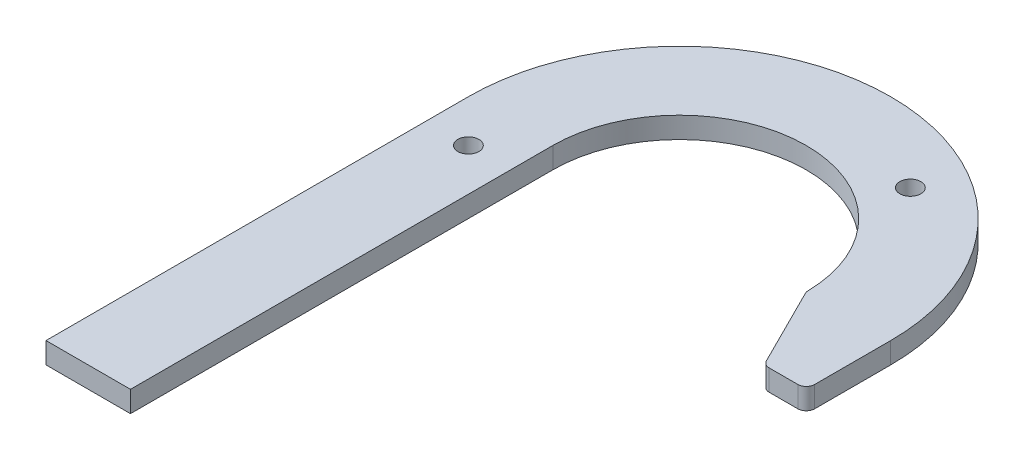
SolidWorks part; units mm, degrees
ref_plane "Front Plane" through (0, 0, 0) normal (0, 0, 1) x (1, 0, 0)
ref_plane "Top Plane" through (0, 0, 0) normal (0, 1, 0) x (1, 0, 0)
ref_plane "Right Plane" through (0, 0, 0) normal (1, 0, 0) x (0, 0, -1)
ref_plane "Plane1" through (0, 6.35, 0) normal (0, 1, 0) x (1, 0, 0)
sketch "Sketch1" plane through (0, 6.35, 0) normal (0, 1, 0) x (1, 0, 0)
  line L0 (90.4698, 44.1178) -> (99.06, 44.1178)
  line L1 (101.6, 46.6578) -> (101.6, 69.5178)
  line L2 (-25.4, 69.5178) -> (-25.4, -57.4822)
  line L3 (-25.4, -57.4822) -> (0, -57.4822)
  line L4 (0, -57.4822) -> (0, 69.5178)
  line L5 (76.4636, 68.9906) -> (88.198, 45.5218)
  circle A0 centre (64.7438, 112.2707) radius 3.175
  arc A1 (99.06, 44.1178) -> (101.6, 46.6578) centre (99.06, 46.6578) ccw
  arc A2 (101.6, 69.5178) -> (-25.4, 69.5178) centre (38.1, 69.5178) ccw
  arc A3 (0, 69.5178) -> (76.1957, 70.0885) centre (38.1, 69.5178) cw
  arc A4 (76.1957, 70.0885) -> (76.4636, 68.9906) centre (78.7354, 70.1265) ccw
  arc A5 (88.198, 45.5218) -> (90.4698, 44.1178) centre (90.4698, 46.6578) ccw
  circle A6 centre (-12.7, 56.8178) radius 3.175
extrude "Boss-Extrude1" add sketch "Sketch1" against normal blind 6.35
